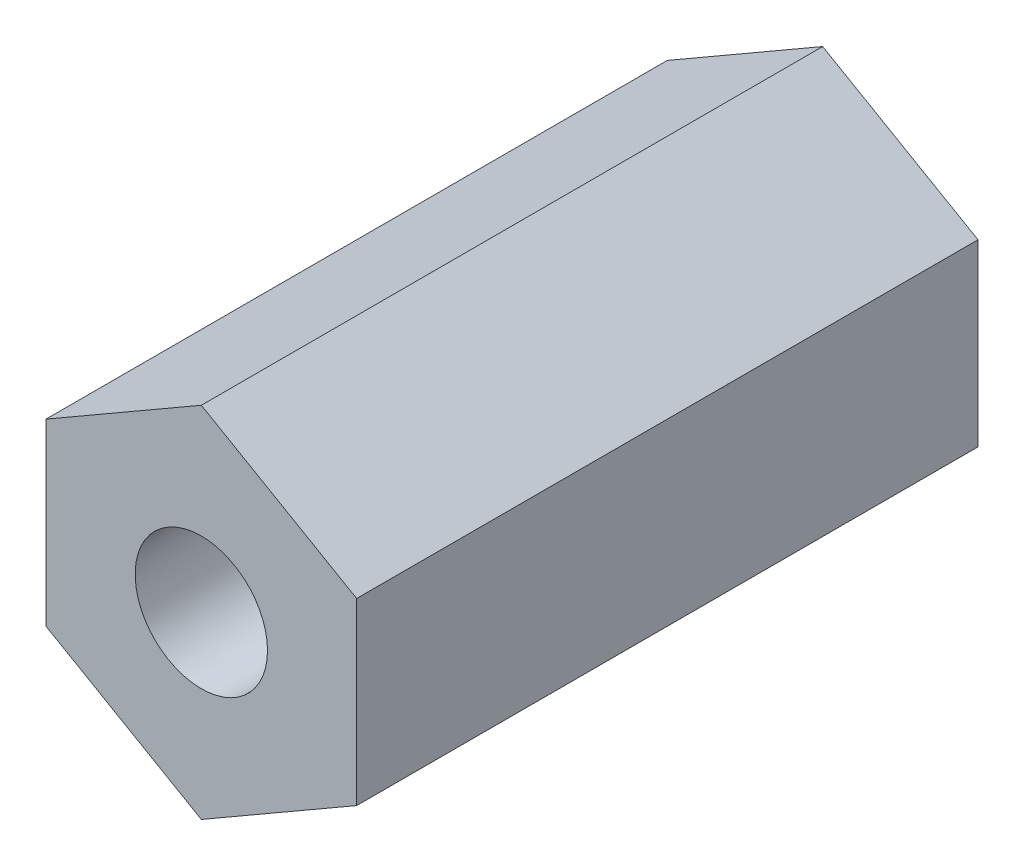
SolidWorks part; units mm, degrees
ref_plane "Front Plane" through (0, 0, 0) normal (0, 0, 1) x (1, 0, 0)
ref_plane "Top Plane" through (0, 0, 0) normal (0, 1, 0) x (1, 0, 0)
ref_plane "Right Plane" through (0, 0, 0) normal (1, 0, 0) x (0, 0, -1)
sketch "Sketch1" plane through (0, 0, 0) normal (0, 0, 1) x (1, 0, 0)
  line L1 (0, 3.6662) -> (-3.175, 1.8331)
  line L2 (-3.175, 1.8331) -> (-3.175, -1.8331)
  line L3 (-3.175, -1.8331) -> (0, -3.6662)
  line L4 (0, -3.6662) -> (3.175, -1.8331)
  line L5 (3.175, -1.8331) -> (3.175, 1.8331)
  line L6 (3.175, 1.8331) -> (0, 3.6662)
  circle A0 centre (0, 0) radius 3.175 construction
extrude "Boss-Extrude1" add sketch "Sketch1" along normal blind 12.7
sketch "Sketch2" plane through (0, 0, 12.7) normal (0, 0, 1) x (1, 0, 0)
  point P0 (0, 0)
hole_wizard "#6-32 Tapped Hole1" positions "Sketch4" profile "Sketch5" tap size "#6-32" standard "ANSI Inch" end condition through all
sketch "Sketch4" plane through (0, 0, 12.7) normal (0, 0, 1) x (1, 0, 0)
  point P0 (0, 0)
sketch "Sketch5" plane through (0, 0, 12.7) normal (1, 0, 0) x (0, -1, 0)
  line L0 (0, 0) -> (0, 12.7)
  line L1 (0, 12.7) -> (1.3525, 12.7)
  line L2 (1.3525, 12.7) -> (1.3525, 0)
  line L5 (1.3525, 0) -> (0, 0)
  line L11 (0, -6.35) -> (0, 107.95) construction
  dimension "Thru Tap Drill Dia." = 2.7051
  dimension "Thru Tap Drill Depth" = 12.7
cosmetic thread "Hole Thread1" parameters "D2"=3.5052
